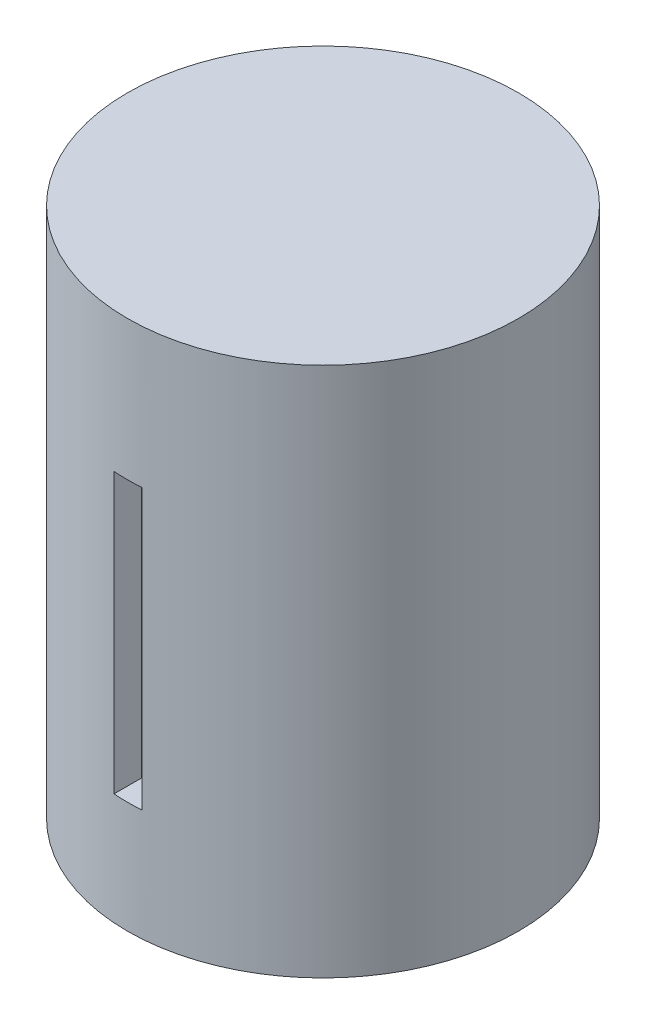
SolidWorks part; units mm, degrees
ref_plane "Front Plane" through (0, 0, 0) normal (0, 0, 1) x (1, 0, 0)
ref_plane "Top Plane" through (0, 0, 0) normal (0, 1, 0) x (1, 0, 0)
ref_plane "Right Plane" through (0, 0, 0) normal (1, 0, 0) x (0, 0, -1)
sketch "Sketch1" plane through (0, 0, 0) normal (0, 1, 0) x (1, 0, 0)
  circle A0 centre (0, 0) radius 14
  dimension "D1" = 28
extrude "Boss-Extrude1" add sketch "Sketch1" along normal blind 38
sketch "Sketch2" plane through (0, 0, 0) normal (0, 1, 0) x (1, 0, 0)
  line L9 (0, 0) -> (0, -14) construction
  line L10 (-1, -15) -> (1, -15)
  line L11 (-1, -15) -> (-1, -12)
  line L12 (-1, -12) -> (1, -12)
  line L13 (1, -15) -> (1, -12)
  line L14 (0, -14) -> (0, -24.1521) construction
  circle A1 centre (0, 0) radius 14 construction
  dimension "D1" = 2
  dimension "D2" = 1
  dimension "D3" = 2
  dimension "D4" = 3
extrude "Cut-Extrude1" cut sketch "Sketch2" along normal blind 20 from offset 8
